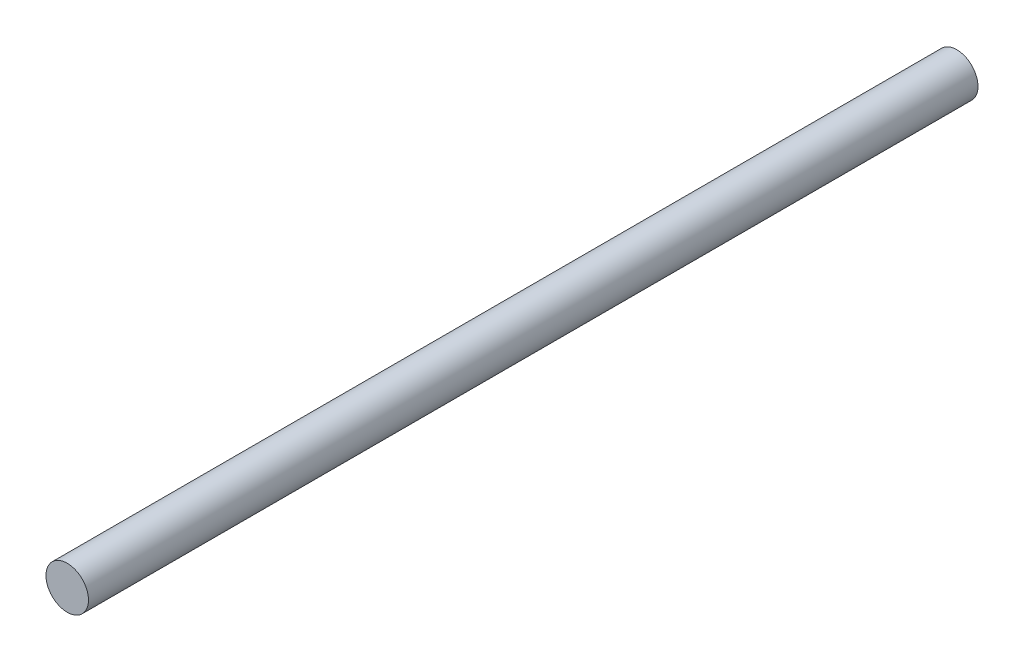
SolidWorks part; units mm, degrees
material "201 Annealed Stainless Steel (SS)"
ref_plane "Front Plane" through (0, 0, 0) normal (0, 0, 1) x (1, 0, 0)
ref_plane "Top Plane" through (0, 0, 0) normal (0, 1, 0) x (1, 0, 0)
ref_plane "Right Plane" through (0, 0, 0) normal (1, 0, 0) x (0, 0, -1)
sketch "Sketch1" plane through (0, 0, 0) normal (0, 0, 1) x (1, 0, 0)
  circle A0 centre (0, 0) radius 2.33
  dimension "D1" = 4.66
extrude "Boss-Extrude1" add sketch "Sketch1" along normal blind 97.5
